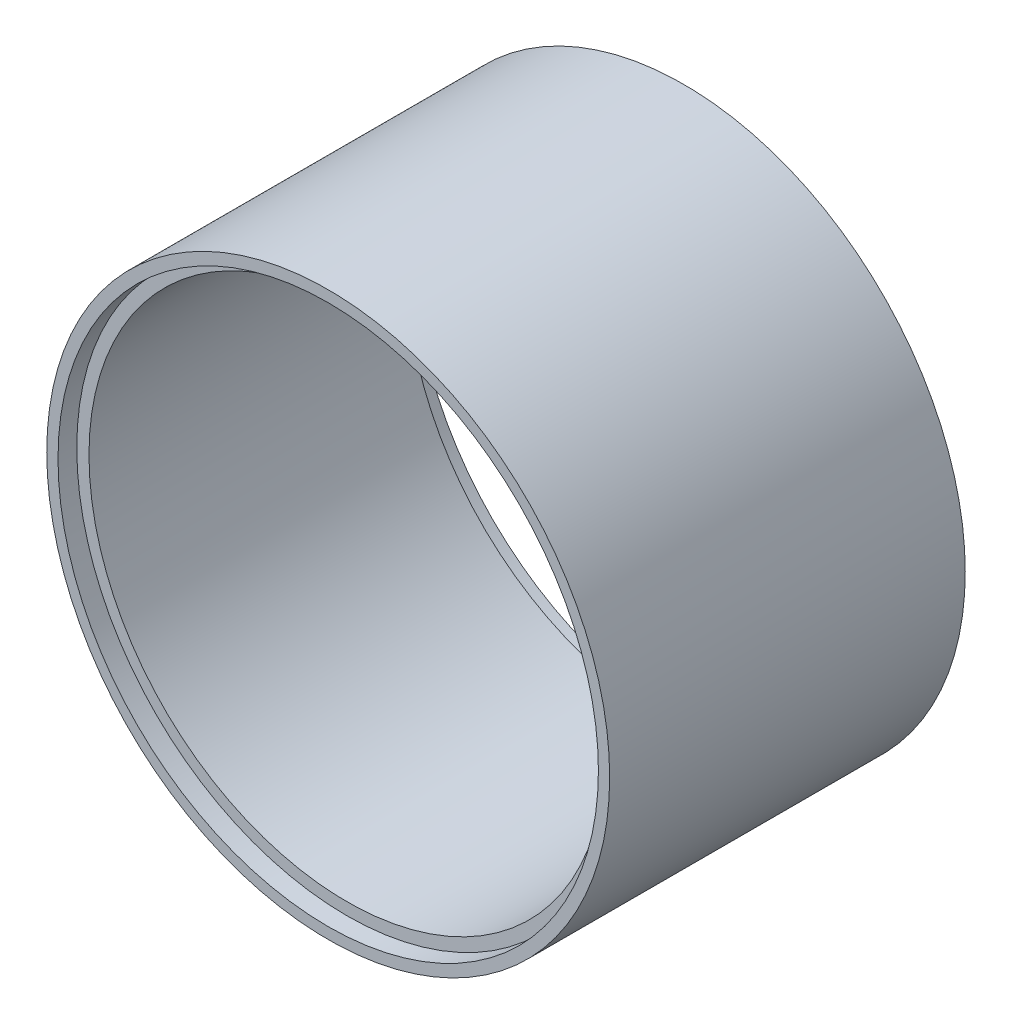
SolidWorks part; units mm, degrees
ref_plane "Front Plane" through (0, 0, 0) normal (0, 0, 1) x (1, 0, 0)
ref_plane "Top Plane" through (0, 0, 0) normal (0, 1, 0) x (1, 0, 0)
ref_plane "Right Plane" through (0, 0, 0) normal (1, 0, 0) x (0, 0, -1)
sketch "Sketch1" plane through (0, 0, 0) normal (0, 0, 1) x (1, 0, 0)
  circle A0 centre (0, -108.5) radius 30 construction
  circle A1 centre (0, -108.5) radius 30
  circle A2 centre (0, -108.5) radius 27.5 construction
  circle A3 centre (0, -108.5) radius 27.5
extrude "Boss-Extrude1" add sketch "Sketch1" against normal up to vertex (39.9 mm away) from vertex at -2
sketch "Sketch2" plane through (0, 0, -2) normal (0, 0, 1) x (1, 0, 0)
  circle A0 centre (0, -108.5) radius 28.8 construction
  circle A1 centre (0, -108.5) radius 28.8
extrude "Cut-Extrude1" cut sketch "Sketch2" against normal up to vertex (2 mm away)
sketch "Sketch3" plane through (0, 0, -39.9) normal (0, 0, -1) x (-1, 0, 0)
  circle A0 centre (0, -108.5) radius 28.8 construction
  circle A1 centre (0, -108.5) radius 28.8
extrude "Cut-Extrude2" cut sketch "Sketch3" against normal up to vertex (2 mm away)
sketch "Sketch4" plane through (0, 0, 0) normal (1, 0, 0) x (0, 0, -1)
  line L2 (20.95, -83.75) -> (18.45, -83.75)
  line L4 (37.9, -81) -> (4, -81) construction
  line L5 (37.9, -81) -> (4, -81) construction
  line L6 (20.95, -81) -> (20.95, -78.5) construction
  line L8 (39.9, -78.5) -> (2, -78.5) construction
  line L10 (20.95, -79.75) -> (20.95, -83.75)
  line L11 (20.95, -79.75) -> (18.45, -83.75)
  dimension "D1" = 2.5
  dimension "D2" = 4
revolve "Revolve1" add sketch "Sketch4" angle 360 about L10
sketch "Sketch5" plane through (0, 0, -2) normal (0, 0, 1) x (1, 0, 0)
  circle A0 centre (0, -108.5) radius 26
  circle A1 centre (0, -108.5) radius 27.5 construction
  dimension "D1" = 1.5
extrude "Cut-Extrude3" cut sketch "Sketch5" against normal through all
